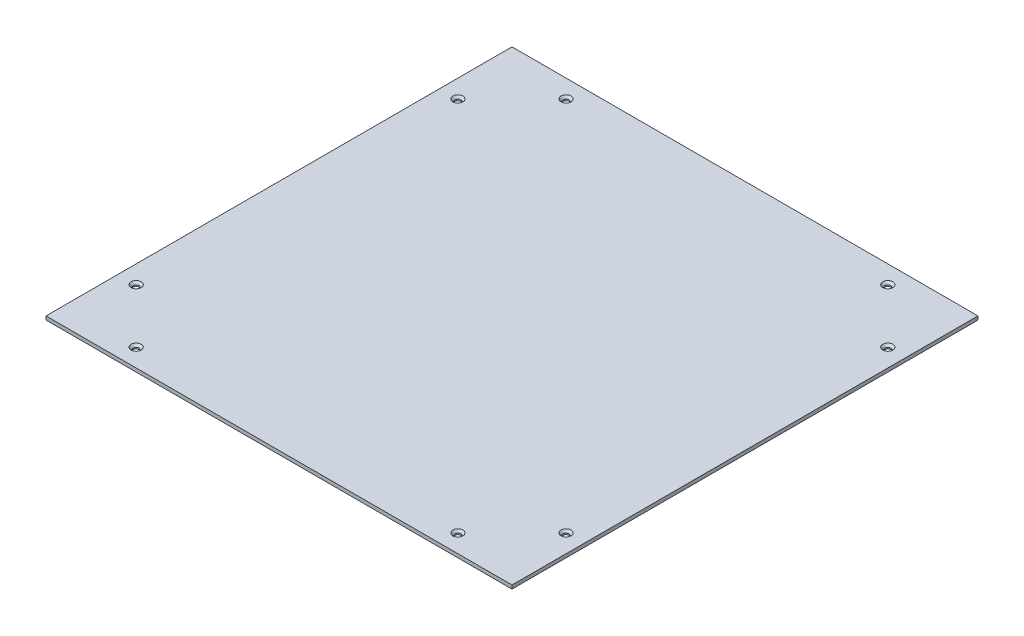
SolidWorks part; units mm, degrees
material "Glass"
ref_plane "Front Plane" through (0, 0, 0) normal (0, 0, 1) x (1, 0, 0)
ref_plane "Top Plane" through (0, 0, 0) normal (0, 1, 0) x (1, 0, 0)
ref_plane "Right Plane" through (0, 0, 0) normal (1, 0, 0) x (0, 0, -1)
sketch "Sketch1" plane through (0, 0, 0) normal (0, 1, 0) x (1, 0, 0)
  line L1 (-323, 323) -> (323, 323)
  line L2 (-323, 323) -> (-323, -323)
  line L3 (-323, -323) -> (323, -323)
  line L4 (323, 323) -> (323, -323)
  line L5 (-323, 323) -> (323, -323) construction
  line L6 (-323, -323) -> (323, 323) construction
  point P0 (0, 0)
  dimension "Largura" = 646
  dimension "Profundidade" = 646
extrude "Boss-Extrude1" add sketch "Sketch1" along normal blind 5
sketch "Sketch2" plane through (0, 5, 0) normal (0, 1, 0) x (1, 0, 0)
  line L0 (-323, -323) -> (323, -323) construction
  line L1 (-323, 323) -> (-323, -323) construction
  line L2 (0, 323) -> (0, -323) construction
  line L3 (323, 323) -> (-323, 323) construction
  line L4 (-323, 0) -> (323, 0) construction
  line L5 (323, -323) -> (323, 323) construction
  circle A0 centre (-223, -298) radius 4
  circle A1 centre (223, -298) radius 4
  circle A2 centre (-298, -223) radius 4
  circle A3 centre (298, -223) radius 4
  circle A4 centre (298, 223) radius 4
  circle A5 centre (223, 298) radius 4
  circle A6 centre (-223, 298) radius 4
  circle A7 centre (-298, 223) radius 4
  dimension "D1" = 8
  dimension "D2" = 25
  dimension "D3" = 100
  dimension "D4" = 25
  dimension "D5" = 100
extrude "Cut-Extrude1" cut sketch "Sketch2" against normal through all
chamfer "Chamfer1" distance 3 angle 45 8 edges at (-223, 5, 302) (-298, 5, -227) (-223, 5, -302) (223, 5, -294) (298, 5, -219) (298, 5, 219) (223, 5, 294) (-298, 5, 227)
